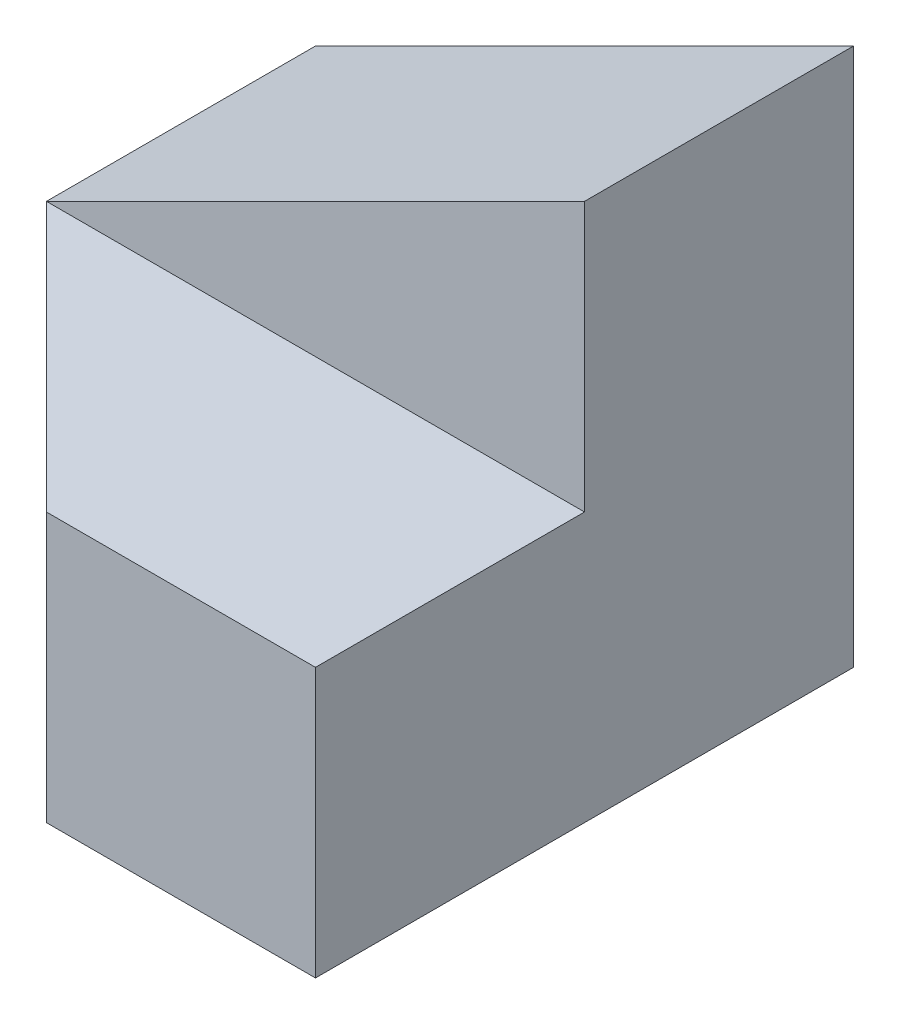
SolidWorks part; units mm, degrees
ref_plane "Front Plane" through (0, 0, 0) normal (0, 0, 1) x (1, 0, 0)
ref_plane "Top Plane" through (0, 0, 0) normal (0, 1, 0) x (1, 0, 0)
ref_plane "Right Plane" through (0, 0, 0) normal (1, 0, 0) x (0, 0, -1)
sketch "Sketch1" plane through (0, 0, 0) normal (0, 0, 1) x (1, 0, 0)
  line L1 (0, 0) -> (40, 0)
  line L2 (0, 0) -> (0, 40)
  line L3 (0, 40) -> (40, 40)
  line L4 (40, 0) -> (40, 40)
  dimension "D1" = 40
  dimension "D2" = 40
extrude "Boss-Extrude1" add sketch "Sketch1" along normal blind 40
sketch "Sketch2" plane through (0, 0, 40) normal (0, 0, 1) x (1, 0, 0)
  line L0 (40, 40) -> (0, 20)
  line L1 (0, 20) -> (0, 40)
  line L2 (0, 40) -> (40, 40)
  dimension "D1" = 20
extrude "Cut-Extrude1" cut sketch "Sketch2" against normal blind 40
sketch "Sketch3" plane through (40, 0, 0) normal (1, 0, 0) x (0, 0, -1)
  line L1 (-40, 40) -> (-20, 40)
  line L2 (-40, 40) -> (-40, 20)
  line L3 (-40, 20) -> (-20, 20)
  line L4 (-20, 40) -> (-20, 20)
  dimension "D1" = 20
  dimension "D2" = 20
extrude "Cut-Extrude2" cut sketch "Sketch3" against normal blind 40
sketch "Sketch4" plane through (0, 20, 0) normal (0, 1, 0) x (1, 0, 0)
  line L0 (0, -20) -> (20, -40)
  line L1 (0, -40) -> (40, -40) construction
  line L2 (20, -40) -> (0, -40)
  line L3 (0, -40) -> (0, -20)
extrude "Cut-Extrude3" cut sketch "Sketch4" against normal blind 40
